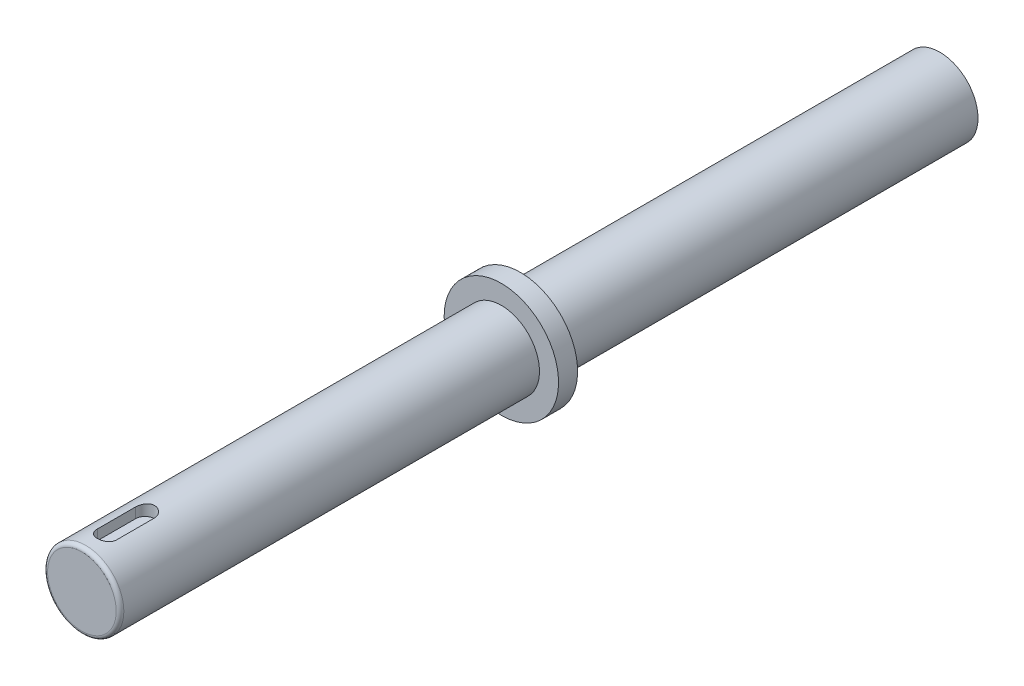
SolidWorks part; units mm, degrees
ref_plane "前视基准面" through (0, 0, 0) normal (0, 0, 1) x (1, 0, 0)
ref_plane "上视基准面" through (0, 0, 0) normal (0, 1, 0) x (1, 0, 0)
ref_plane "右视基准面" through (0, 0, 0) normal (1, 0, 0) x (0, 0, -1)
sketch "草图1" plane through (0, 0, 0) normal (0, 0, 1) x (1, 0, 0)
  circle A0 centre (0, 0) radius 10
  dimension "D1" = 20
extrude "凸台-拉伸1" add sketch "草图1" along normal blind 225
ref_plane "基准面1" through (0, 0, 110) normal (0, 0, -1) x (-1, 0, 0)
sketch "草图2" plane through (0, 0, 110) normal (0, 0, -1) x (-1, 0, 0)
  circle A0 centre (0, 0) radius 15
  dimension "D1" = 30
extrude "凸台-拉伸2" add sketch "草图2" against normal blind 5
ref_plane "基准面2" through (0, 5, 0) normal (0, 1, 0) x (-1, 0, 0)
sketch "草图3" plane through (0, 5, 0) normal (0, 1, 0) x (-1, 0, 0)
  line L1 (0, 208.4314) -> (0, 218.4314) construction
  line L2 (-2.5, 208.4314) -> (-2.5, 218.4314)
  line L3 (2.5, 208.4314) -> (2.5, 218.4314)
  arc A0 (-2.5, 208.4314) -> (2.5, 208.4314) centre (0, 208.4314) ccw
  arc A1 (2.5, 218.4314) -> (-2.5, 218.4314) centre (0, 218.4314) ccw
  point P4 (0, 213.4314)
  dimension "D1" = 10
  dimension "D2" = 5
ref_plane "基准面3" through (0, 7, 0) normal (0, 1, 0) x (-1, 0, 0)
sketch "草图4" plane through (0, 7, 0) normal (0, 1, 0) x (-1, 0, 0)
  line L0 (-2.5, 208.4314) -> (-2.5, 218.4314) construction
  line L1 (2.5, 208.4314) -> (2.5, 218.4314) construction
  line L2 (-2.5, 208.4314) -> (-2.5, 218.4314)
  line L3 (2.5, 208.4314) -> (2.5, 218.4314)
  arc A0 (2.5, 218.4314) -> (-2.5, 218.4314) centre (0, 218.4314) ccw construction
  arc A1 (-2.5, 208.4314) -> (2.5, 208.4314) centre (0, 208.4314) ccw construction
  arc A2 (2.5, 218.4314) -> (-2.5, 218.4314) centre (0, 218.4314) ccw
  arc A3 (-2.5, 208.4314) -> (2.5, 208.4314) centre (0, 208.4314) ccw
extrude "切除-拉伸1" cut sketch "草图4" along normal blind 18
fillet "圆角1" radius 1 1 edges at (10, 0, 225)
